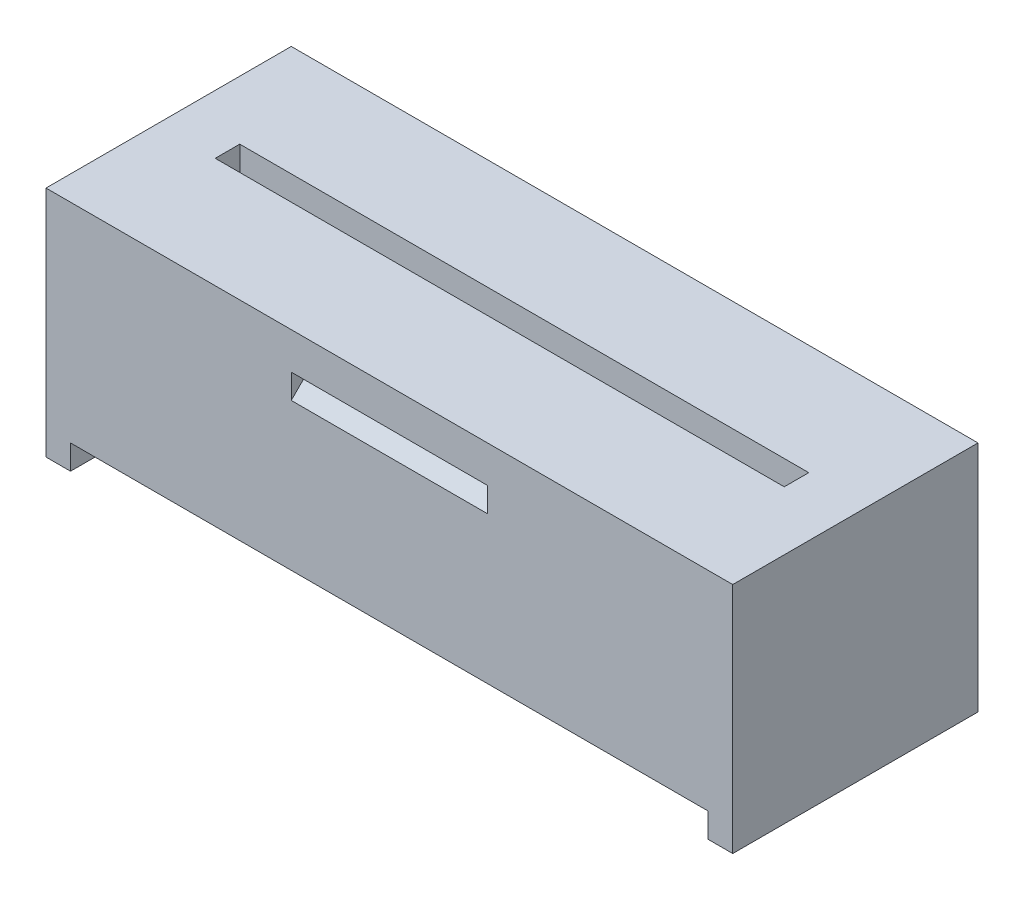
SolidWorks part; units mm, degrees
ref_plane "Přední rovina" through (0, 0, 0) normal (0, 0, 1) x (1, 0, 0)
ref_plane "Horní rovina" through (0, 0, 0) normal (0, 1, 0) x (1, 0, 0)
ref_plane "Pravá rovina" through (0, 0, 0) normal (1, 0, 0) x (0, 0, -1)
sketch "Skica1" plane through (0, 0, 0) normal (0, 0, 1) x (1, 0, 0)
  line L5 (-18.6567, 1.7853) -> (-46.6567, 1.7853)
  line L10 (-18.6567, 1.7853) -> (-18.6567, -6.7147)
  line L11 (-46.6567, 1.7853) -> (-46.6567, -6.7147)
  line L12 (-46.6567, -6.7147) -> (-18.6567, -6.7147)
  dimension "D1" = 8.5
  dimension "D6" = 28
extrude "Přidat vysunutím1" add sketch "Skica1" along normal blind 10 contours L5 L11 L12 L10
sketch "Skica3" plane through (0, -6.7147, 0) normal (0, -1, 0) x (-1, 0, 0)
  line L4 (46.6567, -10) -> (46.6567, 0) construction
  line L5 (46.6567, 0) -> (18.6567, 0) construction
  line L6 (18.6567, -10) -> (18.6567, 0) construction
  circle A4 centre (41.6567, -5) radius 2.6
  circle A5 centre (35.6467, -5) radius 2.6
  circle A6 centre (29.6367, -5) radius 2.6
  circle A7 centre (23.6267, -5) radius 2.6
  dimension "D1" = 5.2
  dimension "D4" = 4
  dimension "D3" = 5
  dimension "D5" = 4.97
  dimension "D2" = 5
extrude "Odebrat vysunutím2" cut sketch "Skica3" against normal blind 7.5
sketch "Skica4" plane through (0, 1.7853, 0) normal (0, 1, 0) x (1, 0, 0)
  line L1 (-44.2567, -4.5) -> (-21.0567, -4.5)
  line L2 (-44.2567, -4.5) -> (-44.2567, -5.5)
  line L3 (-44.2567, -5.5) -> (-21.0567, -5.5)
  line L4 (-21.0567, -4.5) -> (-21.0567, -5.5)
  line L5 (-44.2567, -4.5) -> (-21.0567, -5.5) construction
  line L6 (-44.2567, -5.5) -> (-21.0567, -4.5) construction
  line L7 (-18.6567, -10) -> (-18.6567, 0) construction
  line L8 (-18.6567, -10) -> (-46.6567, -10) construction
  line L9 (-46.6567, -10) -> (-46.6567, 0) construction
  point P0 (-32.6567, -5)
  dimension "D1" = 1
  dimension "D2" = 23.2
  dimension "D3" = 4.5
  dimension "D4" = 2.4
  dimension "D5" = 2.4
extrude "Odebrat vysunutím3" cut sketch "Skica4" against normal blind 1
sketch "Skica5" plane through (0, -6.7147, 0) normal (0, -1, 0) x (-1, 0, 0)
  line L1 (46.6567, -10) -> (45.6567, -10)
  line L2 (46.6567, -10) -> (46.6567, 0)
  line L3 (46.6567, 0) -> (45.6567, 0)
  line L4 (45.6567, -10) -> (45.6567, 0)
  line L5 (18.6567, -10) -> (19.6567, -10)
  line L6 (18.6567, -10) -> (18.6567, 0)
  line L7 (18.6567, 0) -> (19.6567, 0)
  line L8 (19.6567, -10) -> (19.6567, 0)
  dimension "D1" = 10
  dimension "D2" = 1
  dimension "D3" = 10
  dimension "D4" = 1
extrude "Přidat vysunutím2" add sketch "Skica5" along normal blind 1
sketch "Skica9" plane through (-18.6567, 0, 0) normal (1, 0, 0) x (0, 0, -1)
  line L0 (-10, 0.2853) -> (-9, 0.2853)
  line L1 (-10, 1.7853) -> (-10, -7.7147) construction
  line L2 (-9, 0.2853) -> (-10, -0.7147)
  line L3 (-10, -0.7147) -> (-10, 0.2853)
  line L4 (0, 0.2853) -> (-1, 0.2853)
  line L5 (0, 1.7853) -> (0, -7.7147) construction
  line L6 (-1, 0.2853) -> (0, -0.7147)
  line L7 (0, -0.7147) -> (0, 0.2853)
  dimension "D1" = 1
  dimension "D2" = 8
  dimension "D3" = 1
  dimension "D4" = 1
extrude "Odebrat vysunutím5" cut sketch "Skica9" against normal blind 8 from offset 10
